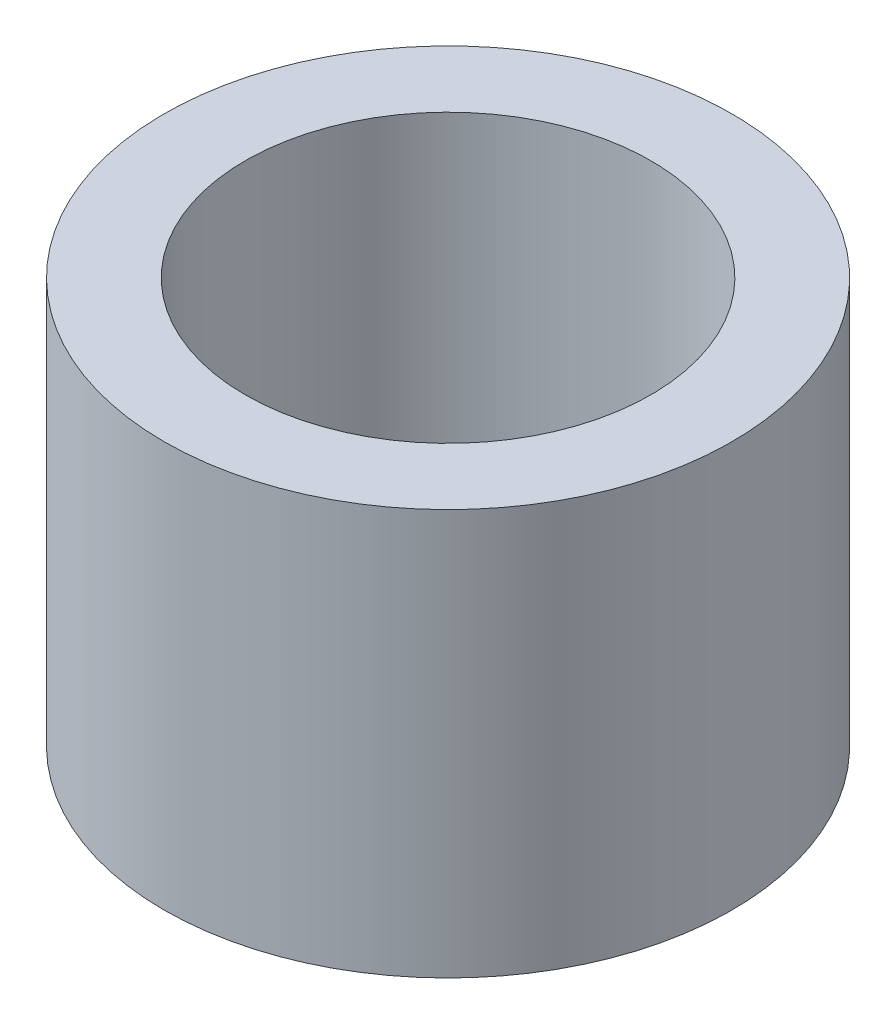
SolidWorks part; units mm, degrees
ref_plane "Front Plane" through (0, 0, 0) normal (0, 0, 1) x (1, 0, 0)
ref_plane "Top Plane" through (0, 0, 0) normal (0, 1, 0) x (1, 0, 0)
ref_plane "Right Plane" through (0, 0, 0) normal (1, 0, 0) x (0, 0, -1)
sketch "Sketch1" plane through (0, 0, 0) normal (0, 1, 0) x (1, 0, 0)
  circle A0 centre (0, 0) radius 2.5
  circle A1 centre (0, 0) radius 3.5
  dimension "D1" = 5
  dimension "D2" = 7
extrude "Boss-Extrude1" add sketch "Sketch1" along normal blind 5
